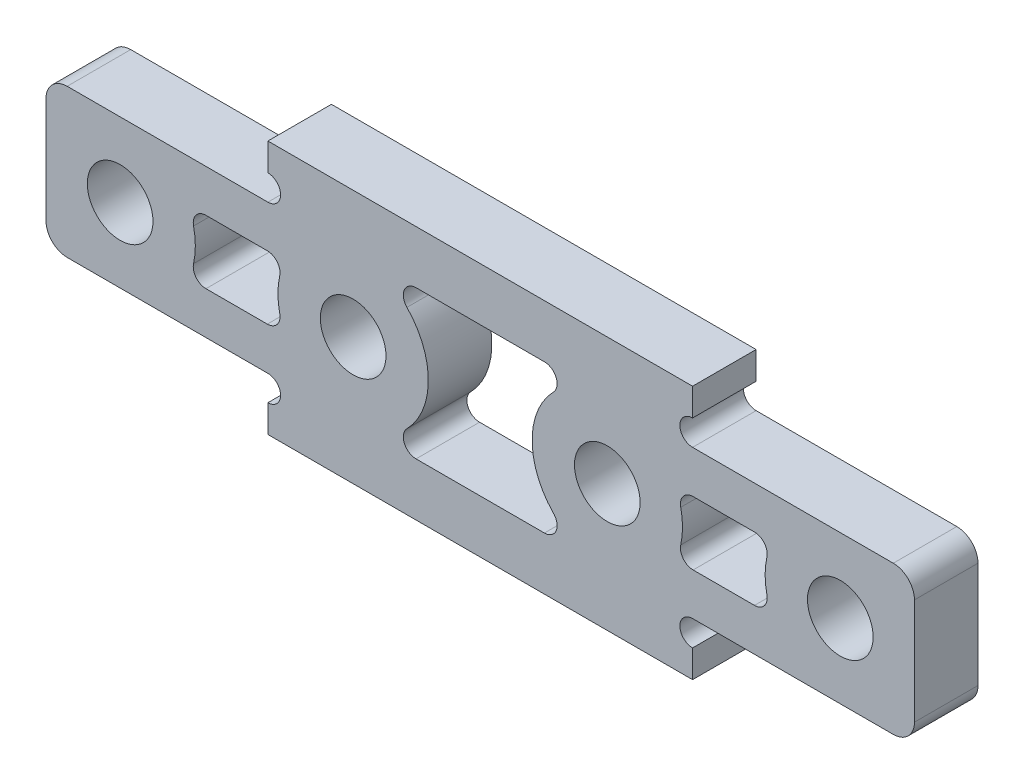
SolidWorks part; units mm, degrees
ref_plane "前视基准面" through (0, 0, 0) normal (0, 0, 1) x (1, 0, 0)
ref_plane "上视基准面" through (0, 0, 0) normal (0, 1, 0) x (1, 0, 0)
ref_plane "右视基准面" through (0, 0, 0) normal (1, 0, 0) x (0, 0, -1)
sketch "草图1" plane through (0, 0, 0) normal (0, 0, 1) x (1, 0, 0)
  line L0 (-20.5, 3.5) -> (-10.025, 3.5)
  line L1 (-10.025, 3.5) -> (-10.025, 6)
  line L2 (-10.025, 6) -> (10.025, 6)
  line L3 (0, 6) -> (0, -6) construction
  line L4 (10.025, -6) -> (-10.025, -6)
  line L5 (-10.025, -6) -> (-10.025, -3.5)
  line L6 (-10.025, -3.5) -> (-20.5, -3.5)
  line L7 (-20.5, -3.5) -> (-20.5, 3.5)
  line L8 (-20.5, 0) -> (-17, 0) construction
  line L9 (-17, 0) -> (-6, 0) construction
  line L10 (10.025, -6) -> (10.025, -3.5)
  line L11 (10.025, 3.5) -> (10.025, 6)
  line L12 (20.5, 3.5) -> (10.025, 3.5)
  line L13 (10.025, -3.5) -> (20.5, -3.5)
  line L14 (20.5, -3.5) -> (20.5, 3.5)
  circle A0 centre (-17, 0) radius 1.55
  circle A1 centre (-6, 0) radius 1.55
  circle A2 centre (6, 0) radius 1.55
  circle A3 centre (17, 0) radius 1.55
  point P14 (-11.5, 0)
  dimension "D2" = 3.5
  dimension "D4" = 3.1
  dimension "D1" = 7
  dimension "D3" = 11
  dimension "D5" = 23
  dimension "D6" = 20.05
  dimension "D7" = 12
extrude "凸台-拉伸1" add sketch "草图1" along normal mid plane 3
sketch "草图2" plane through (0, 0, 1.5) normal (0, 0, 1) x (1, 0, 0)
  line L0 (-10.025, 6) -> (-10.025, 3.5) construction
  line L1 (-10.025, -3.5) -> (-10.025, -6) construction
  line L2 (10.025, 3.5) -> (10.025, 6) construction
  line L3 (10.025, -6) -> (10.025, -3.5) construction
  circle A0 centre (-10.025, 4.1) radius 0.6
  circle A1 centre (-10.025, -4.1) radius 0.6
  circle A2 centre (10.025, 4.1) radius 0.6
  circle A3 centre (10.025, -4.1) radius 0.6
  dimension "D1" = 1.2
extrude "切除-拉伸1" cut sketch "草图2" against normal through all both and the other way through all
fillet "圆角1" radius 1 4 edges at (20.5, -3.5, 0) (20.5, 3.5, 0) (-20.5, -3.5, 0) (-20.5, 3.5, 0)
sketch "草图4" plane through (0, 0, 1.5) normal (0, 0, 1) x (1, 0, 0)
  line L0 (-13.7825, 1.5) -> (-9.2175, 1.5)
  line L1 (-13.7825, -1.5) -> (-9.2175, -1.5)
  line L2 (-10.025, 3.5) -> (-19.5, 3.5) construction
  line L3 (-5.4063, 3.5) -> (5.4063, 3.5)
  line L4 (0, 3.5) -> (0, -3.5) construction
  line L5 (5.4063, -3.5) -> (-5.4063, -3.5)
  line L6 (10.025, 6) -> (-10.025, 6) construction
  line L7 (13.7825, 1.5) -> (9.2175, 1.5)
  line L8 (13.7825, -1.5) -> (9.2175, -1.5)
  arc A0 (-13.7825, -1.5) -> (-13.7825, 1.5) centre (-17, 0) ccw
  arc A1 (-9.2175, 1.5) -> (-9.2175, -1.5) centre (-6, 0) ccw
  circle A2 centre (-17, 0) radius 1.55 construction
  arc A3 (-5.4063, -3.5) -> (-5.4063, 3.5) centre (-6, 0) ccw
  circle A4 centre (-6, 0) radius 1.55 construction
  arc A5 (5.4063, -3.5) -> (5.4063, 3.5) centre (6, 0) cw
  arc A6 (13.7825, -1.5) -> (13.7825, 1.5) centre (17, 0) cw
  arc A7 (9.2175, 1.5) -> (9.2175, -1.5) centre (6, 0) cw
  point P11 (0, 0)
  dimension "D1" = 2
  dimension "D4" = 2
  dimension "D2" = 2
  dimension "D3" = 2.5
extrude "切除-拉伸2" cut sketch "草图4" against normal through all
fillet "圆角2" radius 0.6 12 edges at (13.7825, -1.5, 0) (9.2175, -1.5, 0) (9.2175, 1.5, 0) (13.7825, 1.5, 0) (5.4063, 3.5, 0) (5.4063, -3.5, 0) (-5.4063, -3.5, 0) (-5.4063, 3.5, 0) (-13.7825, 1.5, 0) (-9.2175, -1.5, 0) (-13.7825, -1.5, 0) (-9.2175, 1.5, 0)
